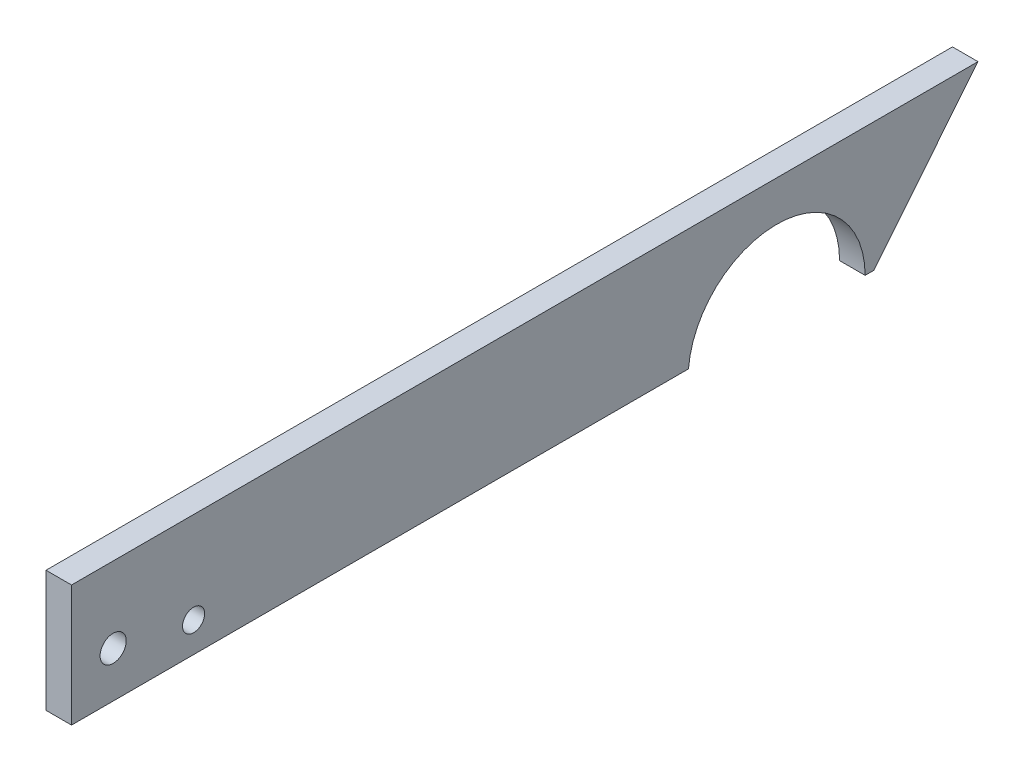
SolidWorks part; units mm, degrees
ref_plane "Front Plane" through (0, 0, 0) normal (0, 0, 1) x (1, 0, 0)
ref_plane "Top Plane" through (0, 0, 0) normal (0, 1, 0) x (1, 0, 0)
ref_plane "Right Plane" through (0, 0, 0) normal (1, 0, 0) x (0, 0, -1)
sketch "Sketch1" plane through (0, 0, 0) normal (1, 0, 0) x (0, 0, -1)
  line L0 (-175.3536, 32) -> (50.0713, 32)
  line L2 (24.1527, 0) -> (22, 0)
  line L9 (-175.3536, 1.8193) -> (-21.9246, 1.8193)
  line L10 (-175.3536, 32) -> (-175.3536, 1.8193)
  line L13 (24.1527, 0) -> (50.0713, 32)
  arc A0 (-21.9246, 1.8193) -> (22, 0) centre (0, 0) cw
  circle A1 centre (-165, 13.1797) radius 3.25
  circle A2 centre (-145, 9.2871) radius 2.75
  point P2 (32, 0)
  point P7 (0, 0)
  point P10 (24.1527, 0)
  point P11 (50.0713, 32)
  dimension "D1" = 6.5
  dimension "D6" = 22
  dimension "D2" = 32
  dimension "D4" = 5.5
  dimension "D3" = 165
  dimension "D7" = 20
extrude "Boss-Extrude1" add sketch "Sketch1" along normal blind 6.35
